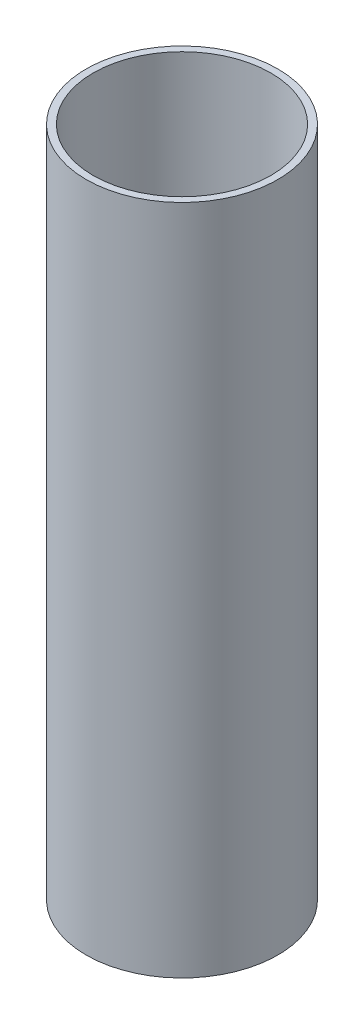
SolidWorks part; units mm, degrees
ref_plane "Front Plane" through (0, 0, 0) normal (0, 0, 1) x (1, 0, 0)
ref_plane "Top Plane" through (0, 0, 0) normal (0, 1, 0) x (1, 0, 0)
ref_plane "Right Plane" through (0, 0, 0) normal (1, 0, 0) x (0, 0, -1)
sketch "Sketch1" plane through (0, 0, 0) normal (0, 1, 0) x (1, 0, 0)
  circle A0 centre (0, 0) radius 25.35
  circle A1 centre (0, 0) radius 23.5
  dimension "D1" = 47
  dimension "D2" = 50.7
extrude "Boss-Extrude1" add sketch "Sketch1" along normal blind 177.66
